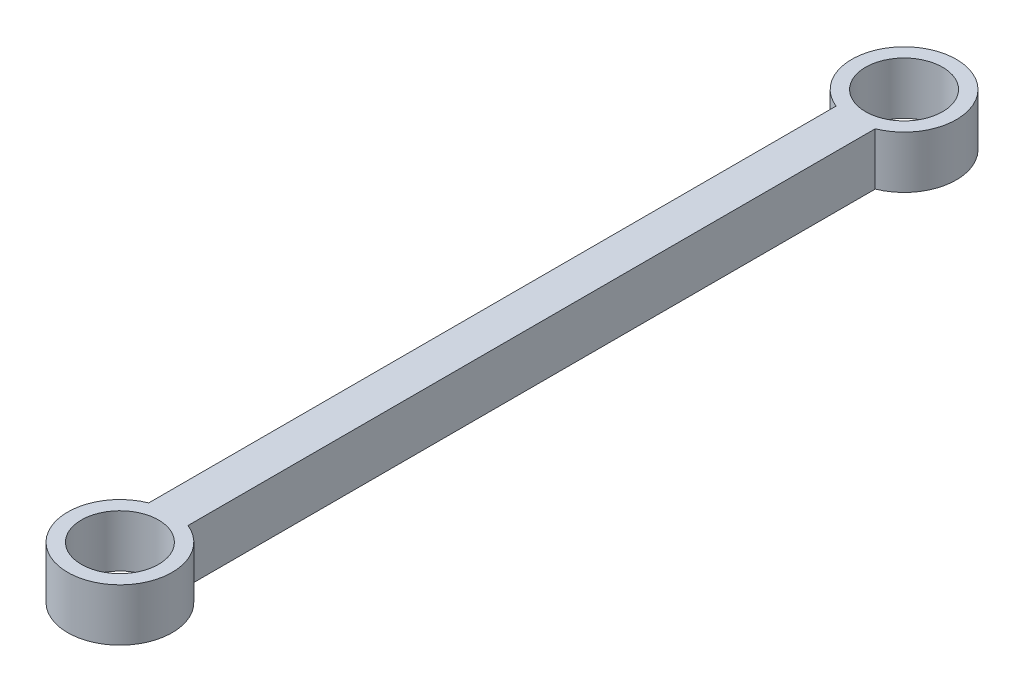
SolidWorks part; units mm, degrees
ref_plane "Front Plane" through (0, 0, 0) normal (0, 0, 1) x (1, 0, 0)
ref_plane "Top Plane" through (0, 0, 0) normal (0, 1, 0) x (1, 0, 0)
ref_plane "Right Plane" through (0, 0, 0) normal (1, 0, 0) x (0, 0, -1)
sketch "Sketch1" plane through (0, 0, 0) normal (0, 1, 0) x (1, 0, 0)
  line L0 (0, 0) -> (0, 60) construction
  line L1 (-1.5, 56.2919) -> (-1.5, 3.7081)
  line L2 (1.5, 56.2919) -> (1.5, 3.7081)
  circle A0 centre (0, 60) radius 2.95
  circle A1 centre (0, 0) radius 2.95
  arc A2 (1.5, 56.2919) -> (-1.5, 56.2919) centre (0, 60) ccw
  arc A3 (-1.5, 3.7081) -> (1.5, 3.7081) centre (0, 0) ccw
  dimension "D2" = 5.9
  dimension "D3" = 5.9
  dimension "D4" = 8
  dimension "D5" = 8
  dimension "D1" = 60
  dimension "D6" = 1.5
  dimension "D7" = 1.5
extrude "Boss-Extrude1" add sketch "Sketch1" along normal blind 4
